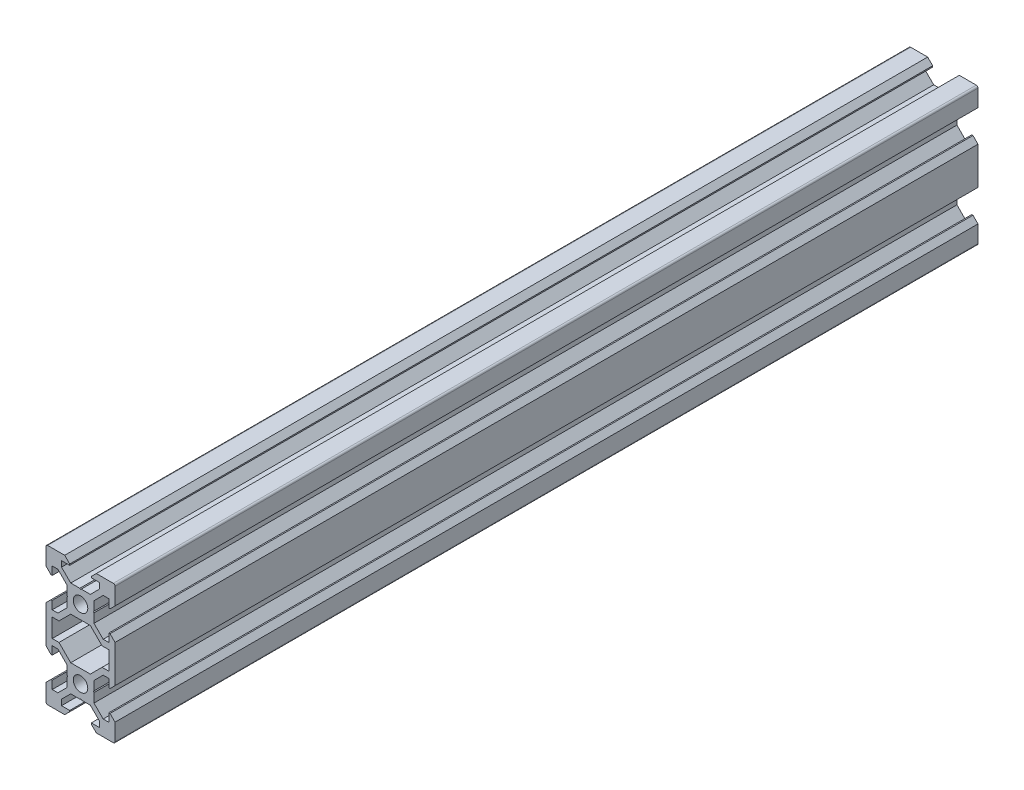
SolidWorks part; units mm, degrees
material "6061-T6 (SS)"
ref_plane "Front Plane" through (0, 0, 0) normal (0, 0, 1) x (1, 0, 0)
ref_plane "Top Plane" through (0, 0, 0) normal (0, 1, 0) x (1, 0, 0)
ref_plane "Right Plane" through (0, 0, 0) normal (1, 0, 0) x (0, 0, -1)
sketch "Sketch1" plane through (0, 0, 0) normal (0, 0, 1) x (1, 0, 0)
  line L0 (0, 0) -> (10, 0) construction
  line L1 (9.5, -20) -> (-9.5, -20)
  line L2 (10, -19.5) -> (10, 19.5)
  line L3 (9.5, 20) -> (-9.5, 20)
  line L4 (-10, -19.5) -> (-10, 19.5)
  line L5 (10, -20) -> (-10, 20) construction
  line L6 (10, 20) -> (-10, -20) construction
  circle A0 centre (0, 10) radius 2.1
  circle A1 centre (0, -10) radius 2.1
  arc A2 (-9.5, -20) -> (-10, -19.5) centre (-9.5, -19.5) cw
  arc A3 (9.5, -20) -> (10, -19.5) centre (9.5, -19.5) ccw
  arc A4 (10, 19.5) -> (9.5, 20) centre (9.5, 19.5) ccw
  arc A5 (-9.5, 20) -> (-10, 19.5) centre (-9.5, 19.5) ccw
  point P0 (0, 0)
  line B0 (0, 10) -> (0, 20) construction
  line B1 (0, 13.69) -> (-0.21, 13.9)
  line B2 (-0.21, 13.9) -> (-2.8393, 13.9)
  line B3 (-2.8393, 13.9) -> (-5.5, 16.5607)
  line B4 (-5.5, 16.5607) -> (-5.5, 18.2)
  line B5 (-5.5, 18.2) -> (-3.125, 18.2)
  line B6 (-3.125, 18.2) -> (-3.125, 18.545)
  line B7 (-3.125, 18.545) -> (-4.58, 20)
  line B8 (-4.58, 20) -> (4.58, 20)
  line B9 (0, 10) -> (-5.9132, 15.9132) construction
  line B10 (3.125, 18.545) -> (4.58, 20)
  line B11 (3.125, 18.2) -> (3.125, 18.545)
  line B12 (5.5, 18.2) -> (3.125, 18.2)
  line B13 (5.5, 16.5607) -> (5.5, 18.2)
  line B14 (2.8393, 13.9) -> (5.5, 16.5607)
  line B15 (0.21, 13.9) -> (2.8393, 13.9)
  line B16 (0, 13.69) -> (0.21, 13.9)
  line B17 (0, 10) -> (-10, 10) construction
  line B18 (-3.69, 10) -> (-3.9, 9.79)
  line B19 (-3.9, 9.79) -> (-3.9, 7.1607)
  line B20 (-3.9, 7.1607) -> (-6.5607, 4.5)
  line B21 (-6.5607, 4.5) -> (-8.2, 4.5)
  line B22 (-8.2, 4.5) -> (-8.2, 6.875)
  line B23 (-8.2, 6.875) -> (-8.545, 6.875)
  line B24 (-8.545, 6.875) -> (-10, 5.42)
  line B25 (-10, 5.42) -> (-10, 14.58)
  line B26 (0, 10) -> (-5.9132, 4.0868) construction
  line B27 (-8.545, 13.125) -> (-10, 14.58)
  line B28 (-8.2, 13.125) -> (-8.545, 13.125)
  line B29 (-8.2, 15.5) -> (-8.2, 13.125)
  line B30 (-6.5607, 15.5) -> (-8.2, 15.5)
  line B31 (-3.9, 12.8393) -> (-6.5607, 15.5)
  line B32 (-3.9, 10.21) -> (-3.9, 12.8393)
  line B33 (-3.69, 10) -> (-3.9, 10.21)
  line B34 (0, -10) -> (-10, -10) construction
  line B35 (-3.69, -10) -> (-3.9, -10.21)
  line B36 (-3.9, -10.21) -> (-3.9, -12.8393)
  line B37 (-3.9, -12.8393) -> (-6.5607, -15.5)
  line B38 (-6.5607, -15.5) -> (-8.2, -15.5)
  line B39 (-8.2, -15.5) -> (-8.2, -13.125)
  line B40 (-8.2, -13.125) -> (-8.545, -13.125)
  line B41 (-8.545, -13.125) -> (-10, -14.58)
  line B42 (-10, -14.58) -> (-10, -5.42)
  line B43 (0, -10) -> (-5.9132, -15.9132) construction
  line B44 (-8.545, -6.875) -> (-10, -5.42)
  line B45 (-8.2, -6.875) -> (-8.545, -6.875)
  line B46 (-8.2, -4.5) -> (-8.2, -6.875)
  line B47 (-6.5607, -4.5) -> (-8.2, -4.5)
  line B48 (-3.9, -7.1607) -> (-6.5607, -4.5)
  line B49 (-3.9, -9.79) -> (-3.9, -7.1607)
  line B50 (-3.69, -10) -> (-3.9, -9.79)
  line B51 (0, -10) -> (0, -20) construction
  line B52 (0, -13.69) -> (0.21, -13.9)
  line B53 (0.21, -13.9) -> (2.8393, -13.9)
  line B54 (2.8393, -13.9) -> (5.5, -16.5607)
  line B55 (5.5, -16.5607) -> (5.5, -18.2)
  line B56 (5.5, -18.2) -> (3.125, -18.2)
  line B57 (3.125, -18.2) -> (3.125, -18.545)
  line B58 (3.125, -18.545) -> (4.58, -20)
  line B59 (4.58, -20) -> (-4.58, -20)
  line B60 (0, -10) -> (5.9132, -15.9132) construction
  line B61 (-3.125, -18.545) -> (-4.58, -20)
  line B62 (-3.125, -18.2) -> (-3.125, -18.545)
  line B63 (-5.5, -18.2) -> (-3.125, -18.2)
  line B64 (-5.5, -16.5607) -> (-5.5, -18.2)
  line B65 (-2.8393, -13.9) -> (-5.5, -16.5607)
  line B66 (-0.21, -13.9) -> (-2.8393, -13.9)
  line B67 (0, -13.69) -> (-0.21, -13.9)
  line B68 (0, -10) -> (10, -10) construction
  line B69 (3.69, -10) -> (3.9, -9.79)
  line B70 (3.9, -9.79) -> (3.9, -7.1607)
  line B71 (3.9, -7.1607) -> (6.5607, -4.5)
  line B72 (6.5607, -4.5) -> (8.2, -4.5)
  line B73 (8.2, -4.5) -> (8.2, -6.875)
  line B74 (8.2, -6.875) -> (8.545, -6.875)
  line B75 (8.545, -6.875) -> (10, -5.42)
  line B76 (10, -5.42) -> (10, -14.58)
  line B77 (0, -10) -> (5.9132, -4.0868) construction
  line B78 (8.545, -13.125) -> (10, -14.58)
  line B79 (8.2, -13.125) -> (8.545, -13.125)
  line B80 (8.2, -15.5) -> (8.2, -13.125)
  line B81 (6.5607, -15.5) -> (8.2, -15.5)
  line B82 (3.9, -12.8393) -> (6.5607, -15.5)
  line B83 (3.9, -10.21) -> (3.9, -12.8393)
  line B84 (3.69, -10) -> (3.9, -10.21)
  line B85 (0, 10) -> (10, 10) construction
  line B86 (3.69, 10) -> (3.9, 10.21)
  line B87 (3.9, 10.21) -> (3.9, 12.8393)
  line B88 (3.9, 12.8393) -> (6.5607, 15.5)
  line B89 (6.5607, 15.5) -> (8.2, 15.5)
  line B90 (8.2, 15.5) -> (8.2, 13.125)
  line B91 (8.2, 13.125) -> (8.545, 13.125)
  line B92 (8.545, 13.125) -> (10, 14.58)
  line B93 (10, 14.58) -> (10, 5.42)
  line B94 (0, 10) -> (5.9132, 15.9132) construction
  line B95 (8.545, 6.875) -> (10, 5.42)
  line B96 (8.2, 6.875) -> (8.545, 6.875)
  line B97 (8.2, 4.5) -> (8.2, 6.875)
  line B98 (6.5607, 4.5) -> (8.2, 4.5)
  line B99 (3.9, 7.1607) -> (6.5607, 4.5)
  line B100 (3.9, 9.79) -> (3.9, 7.1607)
  line B101 (3.69, 10) -> (3.9, 9.79)
  line B102 (-8.2, -2.7) -> (-8.2, 2.7)
  line B103 (-8.2, 2.7) -> (-6.2393, 2.7)
  line B104 (-6.2393, 2.7) -> (-2.8393, 6.1)
  line B105 (-2.8393, 6.1) -> (2.8393, 6.1)
  line B106 (0, 6.1) -> (0, 0) construction
  line B107 (0, 0) -> (-8.2, 0) construction
  line B108 (6.2393, 2.7) -> (2.8393, 6.1)
  line B109 (8.2, 2.7) -> (6.2393, 2.7)
  line B110 (8.2, -2.7) -> (8.2, 2.7)
  line B111 (8.2, -2.7) -> (6.2393, -2.7)
  line B112 (6.2393, -2.7) -> (2.8393, -6.1)
  line B113 (-2.8393, -6.1) -> (2.8393, -6.1)
  line B114 (-6.2393, -2.7) -> (-2.8393, -6.1)
  line B115 (-8.2, -2.7) -> (-6.2393, -2.7)
  line B116 (0, 6.1) -> (0, 10) construction
  line B117 (0, 10) -> (-5.0927, 4.9073) construction
  dimension "D4" = 4.2
  dimension "D5" = 0.5
  dimension "D1" = 20
  dimension "D2" = 40
  dimension "D3" = 20
sketch_block_instance "V Slot 1-4"
sketch_block "V Slot 1" parameters "D1"=10, "D2"=11, "D3"=4.3, "D4"=1.8, "D5"=0.21, "D6"=45, "D7"=9.16, "D8"=1.5, "D9"=6.25
sketch_block_instance "V Slot 1-5"
sketch_block_instance "V Slot 1-6"
sketch_block_instance "V Slot 1-7"
sketch_block_instance "V Slot 1-8"
sketch_block_instance "V Slot 1-9"
sketch_block_instance "Center Cutout 1-1"
sketch_block "Center Cutout 1" parameters "D1"=5.4, "D2"=12.2, "D3"=8.2, "D4"=45, "D5"=10, "D6"=1.5
extrude "Boss-Extrude1" add sketch "Sketch1" along normal blind 250 contours B101 B86 B87 B88 B89 B90 B91 B92 L2 A4 L3 B10 B11 B12 B13 B14 B15 B16 B1 B2 B3 B4 B5 B6 B7 A5 L4 B27 B28 B29 B30 B31 B32 B33 B18 B19 B20 B21 B22 B23 B24 B44 B45 B46 B47 B48 B49 B50 B35
